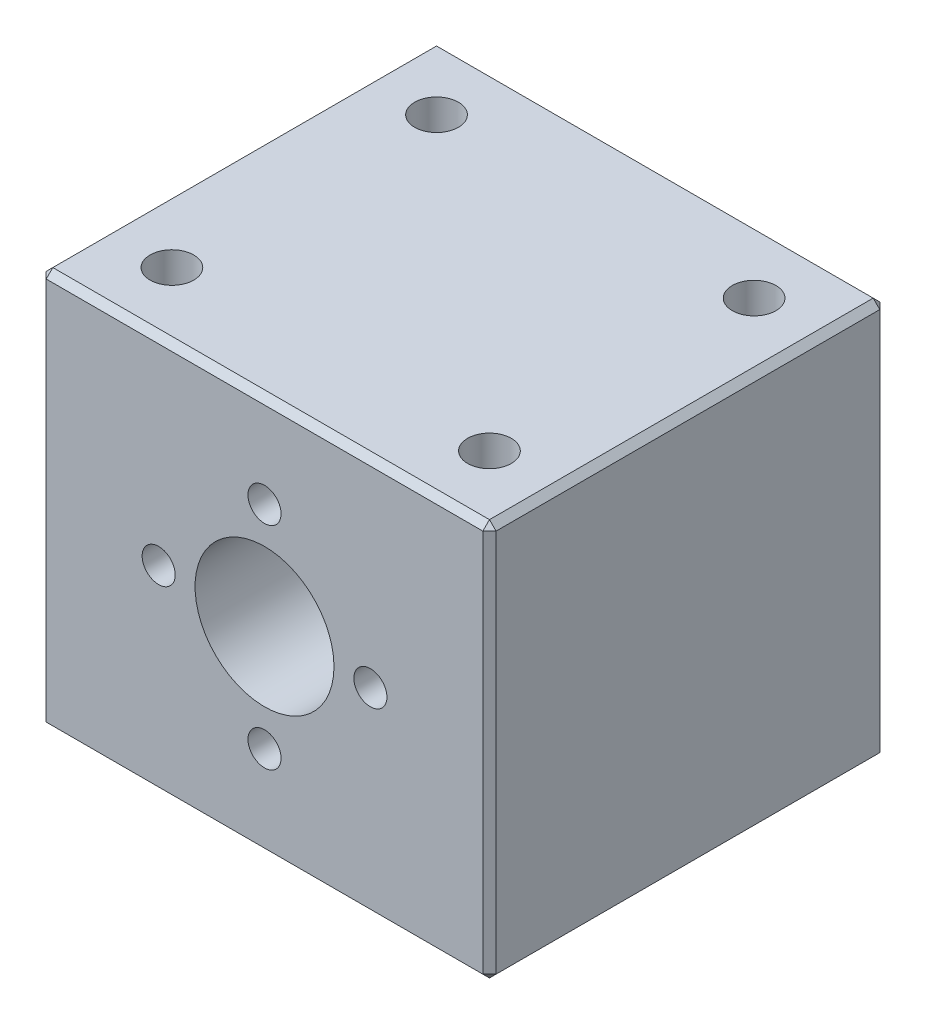
SolidWorks part; units mm, degrees
material "6061 合金"
ref_plane "前基準面" through (0, 0, 0) normal (0, 0, 1) x (1, 0, 0)
ref_plane "上基準面" through (0, 0, 0) normal (0, 1, 0) x (1, 0, 0)
ref_plane "右基準面" through (0, 0, 0) normal (1, 0, 0) x (0, 0, -1)
sketch "草圖1" plane through (0, 0, 0) normal (0, 0, 1) x (1, 0, 0)
  line L1 (-17, 15) -> (17, 15)
  line L2 (-17, 15) -> (-17, -15)
  line L3 (-17, -15) -> (17, -15)
  line L4 (17, 15) -> (17, -15)
  line L5 (-17, 15) -> (17, -15) construction
  line L6 (-17, -15) -> (17, 15) construction
  point P0 (0, 0)
  dimension "D1" = 34
  dimension "D2" = 30
extrude "填料-伸長1" add sketch "草圖1" along normal mid plane 30
sketch "草圖3" plane through (0, 0, 15) normal (0, 0, 1) x (1, 0, 0)
  circle A0 centre (0, 0) radius 5.25
  dimension "D1" = 10.5
extrude "除料-伸長1" cut sketch "草圖3" against normal through all
hole_wizard "M3x0.5 螺紋孔1" positions "草圖5" profile "草圖6" tap size "M3x0.5" standard "Ansi Metric"
sketch "草圖5" plane through (0, 0, 15) normal (0, 0, 1) x (1, 0, 0)
  line L3 (-8, 0) -> (8, 0) construction
  line L4 (0, -8) -> (0, 8) construction
  point P2 (8, 0)
  point P6 (-8, 0)
  point P34 (0, 8)
  point P37 (0, -8)
  dimension "D1" = 16
sketch "草圖6" plane through (8, 0, 15) normal (1, 0, 0) x (0, -1, 0)
  line L0 (0, 0) -> (0, 10.7511)
  line L1 (0, 10.7511) -> (1.25, 10)
  line L2 (1.25, 10) -> (1.25, 0)
  line L5 (1.25, 0) -> (0, 0)
  line L10 (0, 10.7511) -> (-1.25, 10) construction
  line L11 (0, -6.35) -> (0, 107.95) construction
  dimension "螺孔鑽直徑" = 2.5
  dimension "螺孔鑽深度" = 10
  dimension "導頭角度" = 118
hole_wizard "M4x0.7 螺紋孔1" positions "草圖7" profile "草圖8" tap size "M4x0.7" standard "Ansi Metric"
sketch "草圖7" plane through (0, 15, 0) normal (0, 1, 0) x (1, 0, 0)
  line L6 (-12, 10) -> (12, 10)
  line L7 (-12, 10) -> (-12, -10)
  line L8 (-12, -10) -> (12, -10)
  line L9 (12, 10) -> (12, -10)
  line L10 (-12, 10) -> (12, -10) construction
  line L11 (-12, -10) -> (12, 10) construction
  point P101 (12, -10)
  point P186 (-12, 10)
  point P187 (-12, -10)
  point P188 (12, 10)
  point P202 (0, 0)
  dimension "D1" = 24
  dimension "D2" = 20
sketch "草圖8" plane through (12, 15, 10) normal (1, 0, 0) x (0, 0, 1)
  line L0 (0, 0) -> (0, 20.9914)
  line L1 (0, 20.9914) -> (1.65, 20)
  line L2 (1.65, 20) -> (1.65, 0)
  line L5 (1.65, 0) -> (0, 0)
  line L10 (0, 20.9914) -> (-1.65, 20) construction
  line L11 (0, -6.35) -> (0, 107.95) construction
  dimension "螺孔鑽直徑" = 3.3
  dimension "螺孔鑽深度" = 20
  dimension "導頭角度" = 118
chamfer "Chamfer1" distance 0.5 angle 45 12 edges at (-17, 15, 0) (-17, 0, 15) (-17, -15, 0) (-17, 0, -15) (17, -15, 0) (0, -15, 15) (17, 0, 15) (0, 15, 15) (17, 15, 0) (0, 15, -15) (17, 0, -15) (0, -15, -15)
